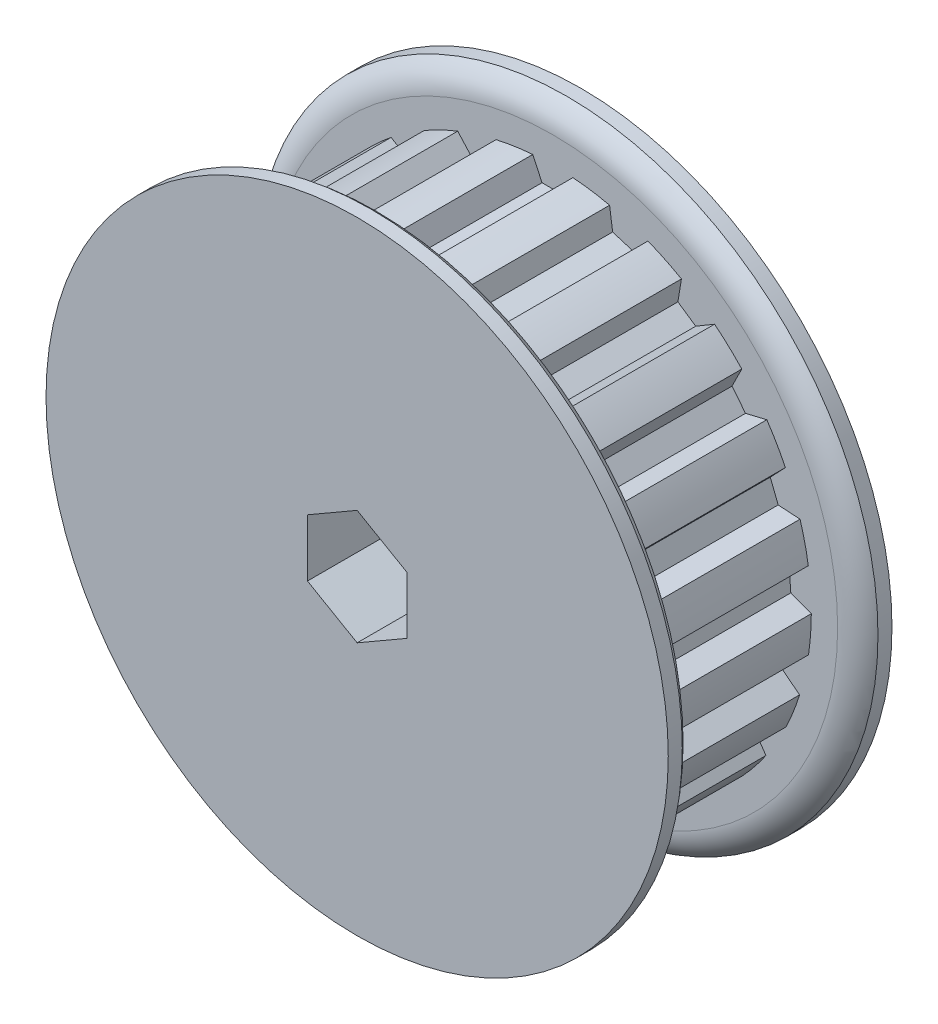
SolidWorks part; units mm, degrees
ref_plane "Front Plane" through (0, 0, 0) normal (0, 0, 1) x (1, 0, 0)
ref_plane "Top Plane" through (0, 0, 0) normal (0, 1, 0) x (1, 0, 0)
ref_plane "Right Plane" through (0, 0, 0) normal (1, 0, 0) x (0, 0, -1)
sketch "Sketch1" plane through (0, 0, 0) normal (0, 0, 1) x (1, 0, 0)
  line L0 (-1.2827, 16.4719) -> (-0.6905, 15.2019)
  line L1 (-0.6905, 15.2019) -> (0.6905, 15.2019)
  line L2 (0.6905, 15.2019) -> (1.2827, 16.4719)
  line L3 (-1.2827, 16.4719) -> (1.2827, 16.4719)
  line L4 (0, 0) -> (0, 15.2019) construction
  line L5 (0, 15.2019) -> (0, 17.4879) construction
  circle A0 centre (0, 0) radius 16.9799 construction
  circle A1 centre (0, 0) radius 19.8882 construction
  circle A2 centre (0, 0) radius 16.5218 construction
  point P6 (0, 16.4719)
  point P11 (0, 16.9799)
  point P13 (0, 19.8882)
  point P14 (0, 16.5218)
  dimension "D1" = 1.016
  dimension "D2" = 0.508
sketch "Sketch2" plane through (0, 0, 0) normal (1, 0, 0) x (0, 0, -1)
  line L0 (-11.1125, 3.175) -> (11.1125, 3.175)
  line L1 (-11.1125, 3.175) -> (-11.1125, 11.9126)
  line L2 (-11.1125, 11.9126) -> (-3.1877, 11.9126)
  line L3 (-3.1877, 11.9126) -> (-3.1877, 19.8882)
  line L4 (-3.1877, 19.8882) -> (-1.397, 19.8882) construction
  line L5 (-1.397, 19.8882) -> (-1.397, 16.5218) construction
  line L6 (-1.397, 16.5218) -> (9.3218, 16.5218)
  line L7 (9.3218, 16.5218) -> (9.3218, 19.8882) construction
  line L8 (9.3218, 19.8882) -> (11.1125, 19.8882) construction
  line L9 (11.1125, 19.8882) -> (11.1125, 3.175)
  line L10 (-11.1125, 0) -> (11.1125, 0) construction
  line L13 (-3.1877, 19.8882) -> (-2.2923, 19.8882)
  line L14 (-1.397, 18.205) -> (-1.397, 16.5218)
  line L15 (9.3218, 16.5218) -> (9.3218, 18.205)
  line L16 (10.2172, 19.8882) -> (11.1125, 19.8882)
  arc A0 (-1.397, 18.205) -> (-2.2923, 19.8882) centre (-3.4269, 18.205) ccw
  arc A1 (9.3218, 18.205) -> (10.2172, 19.8882) centre (11.3517, 18.205) cw
  point P12 (-1.397, 18.205)
  point P14 (-2.2923, 19.8882)
  point P20 (9.3218, 18.205)
  point P21 (10.2172, 19.8882)
  point P25 (9.3218, 0)
  point P26 (-1.397, 0)
  dimension "Bore" = 6.35
  dimension "Hub Dia" = 23.8252
  dimension "Outside Width" = 14.3002
  dimension "Inside Width" = 10.7188
revolve "Revolve1" add sketch "Sketch2" angle 360 mid plane about L10
sketch "Sketch3" plane through (0, 0, 0) normal (0, 0, 1) x (1, 0, 0)
  line L0 (-0.6905, 15.2019) -> (0.6905, 15.2019) construction
  line L1 (0.6905, 15.2019) -> (1.2827, 16.4719) construction
  line L2 (-1.2827, 16.4719) -> (-0.6905, 15.2019) construction
  line L3 (-0.6905, 15.2019) -> (0.6905, 15.2019)
  line L4 (0.6905, 15.2019) -> (1.2827, 16.4719)
  line L5 (-1.2827, 16.4719) -> (-0.6905, 15.2019)
  circle A0 centre (0, 0) radius 16.5218 construction
  arc A1 (1.2827, 16.4719) -> (-1.2827, 16.4719) centre (0, 0) ccw
extrude "Cut-Extrude1" cut sketch "Sketch3" against normal up to vertex (9.3218 mm away) from vertex at 1.397 starting at point (0, 16.5218, 1.397)
pattern_circular "CirPattern1" count 21 over 360 about axis through (0, 0, 0) along (0, 0, 1) of "Cut-Extrude1"
sketch "Sketch4" plane through (0, 0, 0) normal (0, 1, 0) x (1, 0, 0)
  line L0 (0, -3.1877) -> (0, -11.1125) construction
  line L1 (-11.9126, -3.1877) -> (11.9126, -3.1877) construction
  line L2 (-11.9126, -11.1125) -> (11.9126, -11.1125) construction
  circle A0 centre (0, -7.1501) radius 1.5875
  dimension "D1" = 3.175
extrude "Cut-Extrude2" cut sketch "Sketch4" along normal through all
ref_plane "Plane1" through (0, 0, 7.1501) normal (0, 0, 1) x (1, 0, 0)
sketch "Sketch5" plane through (0, 0, 7.1501) normal (0, 0, 1) x (1, 0, 0)
  line L0 (0, 0) -> (0, 11.9126) construction
  line L1 (1.0795, 11.8063) -> (1.5875, 11.2983)
  line L2 (0, 11.8063) -> (1.0795, 11.8063)
  line L3 (0, 11.8063) -> (0, 3.175)
  line L4 (0, 3.175) -> (0.9525, 3.175)
  line L5 (1.5875, 11.2983) -> (1.5875, 3.81)
  line L6 (0.9525, 3.175) -> (1.5875, 3.81)
  circle A0 centre (0, 0) radius 11.9126 construction
  circle A1 centre (0, 0) radius 3.175 construction
  point P7 (1.5875, 3.175)
  point P9 (1.5875, 11.8063)
revolve "Revolve2" add sketch "Sketch5" angle 360 mid plane about L0
sketch "Sketch6" plane through (0, 11.8063, 0) normal (0, 1, 0) x (1, 0, 0)
  line L1 (0, -6.2336) -> (-0.7938, -6.6918)
  line L2 (-0.7938, -6.6918) -> (-0.7937, -7.6084)
  line L3 (-0.7937, -7.6084) -> (0, -8.0666)
  line L4 (0, -8.0666) -> (0.7938, -7.6084)
  line L5 (0.7938, -7.6084) -> (0.7938, -6.6918)
  line L6 (0.7938, -6.6918) -> (0, -6.2336)
  circle A0 centre (0, -7.1501) radius 0.7938 construction
  dimension "D1" = 1.5875
extrude "Cut-Extrude3" cut sketch "Sketch6" against normal blind 1.1906
pattern_circular "CirPattern2" count 2 every 90 about axis through (0, 0, 0) along (0, 0, 1) of "Cut-Extrude2", "Revolve2", "Cut-Extrude3"
sketch "Sketch7" plane through (0, 0, 11.1125) normal (0, 0, 1) x (1, 0, 0)
  line L1 (0, 3.6662) -> (-3.175, 1.8331)
  line L2 (-3.175, 1.8331) -> (-3.175, -1.8331)
  line L3 (-3.175, -1.8331) -> (0, -3.6662)
  line L4 (0, -3.6662) -> (3.175, -1.8331)
  line L5 (3.175, -1.8331) -> (3.175, 1.8331)
  line L6 (3.175, 1.8331) -> (0, 3.6662)
  circle A0 centre (0, 0) radius 3.175 construction
  point P1 (0, 0)
  dimension "D1" = 6.35
extrude "Cut-Extrude4" cut sketch "Sketch7" against normal blind 50.8
sketch "Sketch8" plane through (0, 0, 3.1877) normal (0, 0, 1) x (1, 0, 0)
  circle A0 centre (0, 0) radius 12.7
  dimension "D1" = 25.4
extrude "Cut-Extrude5" cut sketch "Sketch8" along normal blind 50.8
equation "\"D2@Sketch1\" = \"D1@Sketch1\"/2"
equation "\"D1@Sketch4\" = \"Bore@Sketch2\"/2"
equation "\"D1@Sketch6\" = \"D1@Sketch4\"/2"
equation "\"D1@Cut-Extrude3\" = \"D1@Sketch6\"*.75"
